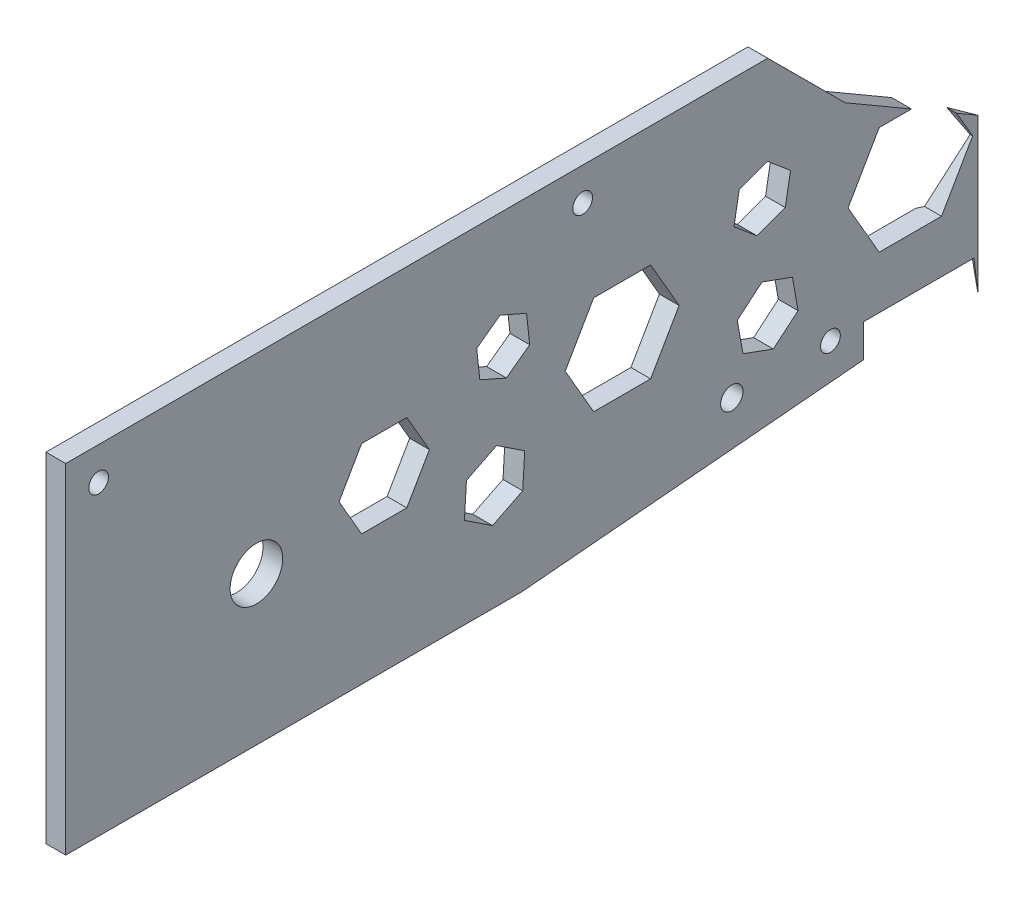
SolidWorks part; units mm, degrees
ref_plane "Alzado" through (0, 0, 0) normal (0, 0, 1) x (1, 0, 0)
ref_plane "Planta" through (0, 0, 0) normal (0, 1, 0) x (1, 0, 0)
ref_plane "Vista lateral" through (0, 0, 0) normal (1, 0, 0) x (0, 0, -1)
sketch "Croquis1" plane through (0, 0, 0) normal (1, 0, 0) x (0, 0, -1)
  line L1 (-80.5, -25.7906) -> (80.5, -25.7906)
  line L2 (-80.5, -25.7906) -> (-80.5, 25.7906)
  line L3 (-80.5, 25.7906) -> (80.5, 25.7906)
  line L4 (80.5, -25.7906) -> (80.5, 25.7906)
  line L5 (-80.5, -25.7906) -> (80.5, 25.7906) construction
  line L6 (-80.5, 25.7906) -> (80.5, -25.7906) construction
  point P0 (0, 0)
  dimension "D1" = 51.5812
  dimension "D2" = 161
extrude "Saliente-Extruir1" add sketch "Croquis1" along normal blind 3
sketch "Croquis2" plane through (3, 0, 0) normal (1, 0, 0) x (0, 0, -1)
  line L0 (-80.5, 25.7906) -> (-75.5, 25.7906) construction
  line L1 (80.5, 25.7906) -> (-80.5, 25.7906) construction
  line L2 (-75.5, 25.7906) -> (-75.5, 20.7906) construction
  line L3 (-75.5, 20.7906) -> (-75.5, -8.2094) construction
  line L4 (-75.5, 20.7906) -> (-51.5, 20.7906) construction
  line L5 (-51.5, 20.7906) -> (-51.5, -3.2094) construction
  circle A0 centre (-75.5, 20.7906) radius 1.5
  circle A1 centre (-1.88, 20.7906) radius 1.5
  circle A2 centre (-51.5, -3.2094) radius 4
  dimension "D1" = 3
  dimension "D4" = 3
  dimension "D5" = 8
  dimension "D2" = 5
  dimension "D3" = 5
  dimension "D6" = 24
  dimension "D7" = 24
extrude "Cortar-Extruir1" cut sketch "Croquis2" against normal up to next
sketch "Croquis3" plane through (0, 0, 0) normal (-1, 0, 0) x (0, 0, 1)
  circle A0 centre (-35.8015, -16.2094) radius 1.5
extrude "Cortar-Extruir2" cut sketch "Croquis3" against normal up to next
sketch "Croquis4" plane through (0, 25.7906, 0) normal (0, 1, 0) x (1, 0, 0)
  line L0 (0, 80.5) -> (3, 80.5)
  line L1 (3, 80.5) -> (3, 58.2418)
  line L2 (3, 80.5) -> (3, -80.5) construction
  line L3 (-2.887, 45.6172) -> (9.4584, 72.092) construction
  line L4 (3, 58.2418) -> (0, 51.8083)
  line L5 (0, 80.5) -> (0, -80.5) construction
  line L6 (0, 51.8083) -> (0, 80.5)
extrude "Cortar-Extruir3" cut sketch "Croquis4" against normal up to next
sketch "Croquis5" plane through (3, 0, 0) normal (1, 0, 0) x (0, 0, -1)
  line L0 (58.2418, -25.7906) -> (58.2418, -21.2094)
  line L1 (58.2418, -25.7906) -> (58.2418, 25.7906) construction
  line L2 (58.2418, -21.2094) -> (40.9109, -21.2094)
  line L3 (40.9109, -21.2094) -> (-11.1291, -25.7906)
  line L4 (-80.5, -25.7906) -> (58.2418, -25.7906) construction
  line L5 (-11.1291, -25.7906) -> (58.2418, -25.7906)
extrude "Cortar-Extruir4" cut sketch "Croquis5" against normal blind 3
sketch "Croquis6" plane through (3, 0, 0) normal (1, 0, 0) x (0, 0, -1)
  line L0 (58.2418, 25.7906) -> (38.0333, 25.7906)
  line L1 (58.2418, 25.7906) -> (-80.5, 25.7906) construction
  line L2 (58.2418, 25.7906) -> (58.2418, 2.2906)
  line L3 (58.2418, -21.2094) -> (58.2418, 25.7906) construction
  line L4 (58.2418, 2.2906) -> (38.0333, 14.0406)
  line L5 (38.0333, 14.0406) -> (38.0333, 25.7906)
  dimension "D1" = 20.2085
  dimension "D2" = 23.5
  dimension "D3" = 11.75
extrude "Cortar-Extruir5" cut sketch "Croquis6" against normal blind 10
sketch "Croquis7" plane through (3, 0, 0) normal (1, 0, 0) x (0, 0, -1)
  line L0 (38.0333, 25.7906) -> (38.0333, 14.0406)
  line L1 (38.0333, 14.0406) -> (26.2535, 25.7906)
  line L2 (38.0333, 25.7906) -> (-80.5, 25.7906) construction
  line L3 (26.2535, -16.2094) -> (26.2535, 30.6106) construction
  line L4 (26.2535, 25.7906) -> (38.0333, 25.7906)
extrude "Cortar-Extruir6" cut sketch "Croquis7" against normal up to next
sketch "Croquis8" plane through (3, 0, 0) normal (1, 0, 0) x (0, 0, -1)
  line L1 (4.1249, -0.035) -> (47.9517, -0.035) construction
  line L2 (-38.9337, -0.035) -> (-35.4978, -5.9861)
  line L3 (-35.4978, -5.9861) -> (-28.626, -5.9861)
  line L4 (4.1249, -0.035) -> (-32.0619, 15.8921) construction
  line L5 (4.1249, -0.035) -> (-34.6803, -19.4238) construction
  line L6 (12.7852, -0.035) -> (8.4551, 7.465)
  line L7 (8.4551, 7.465) -> (-0.2052, 7.465)
  line L8 (-0.2052, 7.465) -> (-4.5353, -0.035)
  line L9 (-4.5353, -0.035) -> (-0.2052, -7.535)
  line L10 (-0.2052, -7.535) -> (8.4551, -7.535)
  line L11 (8.4551, -7.535) -> (12.7852, -0.035)
  line L12 (29.7291, 9.2842) -> (26.2247, 12.2247)
  line L13 (26.2247, 12.2247) -> (21.9258, 10.6601)
  line L14 (21.9258, 10.6601) -> (21.1314, 6.1549)
  line L15 (21.1314, 6.1549) -> (24.6359, 3.2143)
  line L16 (24.6359, 3.2143) -> (28.9347, 4.779)
  line L17 (28.9347, 4.779) -> (29.7291, 9.2842)
  line L18 (-19.8638, -12.0208) -> (-15.5863, -14.8468)
  line L19 (-15.5863, -14.8468) -> (-11.0002, -12.5554)
  line L20 (-11.0002, -12.5554) -> (-10.6916, -7.4379)
  line L21 (-10.6916, -7.4379) -> (-14.969, -4.612)
  line L22 (-14.969, -4.612) -> (-19.5552, -6.9034)
  line L23 (-19.5552, -6.9034) -> (-19.8638, -12.0208)
  line L24 (-17.9983, 9.7022) -> (-17.5194, 5.3254)
  line L25 (-17.5194, 5.3254) -> (-13.4896, 3.5518)
  line L26 (-13.4896, 3.5518) -> (-9.9387, 6.1549)
  line L27 (-9.9387, 6.1549) -> (-10.4175, 10.5316)
  line L28 (-10.4175, 10.5316) -> (-14.4474, 12.3053)
  line L29 (-14.4474, 12.3053) -> (-17.9983, 9.7022)
  line L30 (30.8776, -9.7722) -> (30.0239, -4.9306)
  line L31 (30.0239, -4.9306) -> (25.4041, -3.2491)
  line L32 (25.4041, -3.2491) -> (21.638, -6.4092)
  line L33 (21.638, -6.4092) -> (22.4917, -11.2508)
  line L34 (22.4917, -11.2508) -> (27.1115, -12.9323)
  line L35 (27.1115, -12.9323) -> (30.8776, -9.7722)
  line L54 (-28.626, -5.9861) -> (-25.1901, -0.035)
  line L55 (-25.1901, -0.035) -> (-28.626, 5.9162)
  line L56 (-28.626, 5.9162) -> (-35.4978, 5.9162)
  line L57 (-35.4978, 5.9162) -> (-38.9337, -0.035)
  line L58 (57.4271, -0.035) -> (52.6894, 8.171)
  line L59 (52.6894, 8.171) -> (43.214, 8.171)
  line L60 (43.214, 8.171) -> (38.4763, -0.035)
  line L61 (38.4763, -0.035) -> (43.214, -8.2409)
  line L62 (43.214, -8.2409) -> (52.6894, -8.2409)
  line L63 (52.6894, -8.2409) -> (57.4271, -0.035)
  circle A0 centre (4.1249, -0.035) radius 7.5 construction
  circle A1 centre (25.4303, 7.7195) radius 3.9618 construction
  circle A2 centre (-15.2777, -9.7294) radius 4.4399 construction
  circle A3 centre (-13.9685, 7.9285) radius 3.813 construction
  circle A4 centre (26.2578, -8.0907) radius 4.2576 construction
  circle A5 centre (-32.0619, -0.035) radius 5.9511 construction
  circle A6 centre (47.9517, -0.035) radius 8.2059 construction
extrude "Cortar-Extruir7" cut sketch "Croquis8" against normal up to next
ref_plane "Plano1" through (3, 5.9162, 28.626) normal (0, 0, 1) x (1, 0, 0)
sketch "Croquis10" plane through (3, 0, 0) normal (1, 0, 0) x (0, 0, -1)
  line L0 (-1.8763, 20.7906) -> (41.0903, 20.7906) construction
  line L1 (35.8015, -16.2094) -> (35.8015, 20.7906) construction
  circle A0 centre (35.8015, 20.7906) radius 1.5
  dimension "D1" = 3
sketch "Croquis11" plane through (0, 0, 0) normal (-1, 0, 0) x (0, 0, 1)
  circle A0 centre (-20.8015, -16.2094) radius 1.7
extrude "Cortar-Extruir9" cut sketch "Croquis11" against normal blind 10
sketch "Croquis12" plane through (3, 0, 0) normal (1, 0, 0) x (0, 0, -1)
  line L0 (58.2418, -21.2094) -> (57.6271, -16.2094)
  line L1 (40.9109, -16.2094) -> (65.9109, -16.2094) construction
  line L2 (57.6271, -16.2094) -> (57.6271, -21.2094) construction
  line L3 (57.6271, -16.2094) -> (40.8116, -16.2094)
  line L4 (40.8116, -16.2094) -> (40.8116, -21.2181)
  line L5 (40.9109, -21.2094) -> (-11.1291, -25.7906) construction
  line L6 (40.8116, -21.2181) -> (40.9109, -21.2094)
  line L7 (40.9109, -21.2094) -> (58.2418, -21.2094)
extrude "Cortar-Extruir10" cut sketch "Croquis12" against normal up to next
